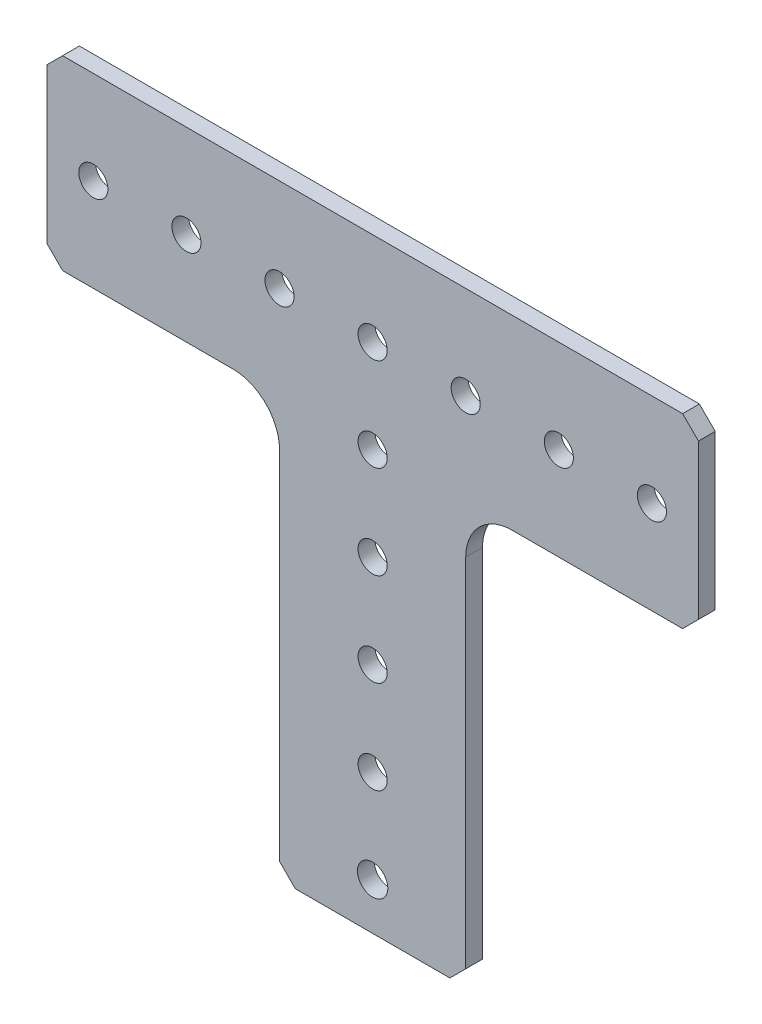
SolidWorks part; units mm, degrees
ref_plane "Front Plane" through (0, 0, 0) normal (0, 0, 1) x (1, 0, 0)
ref_plane "Top Plane" through (0, 0, 0) normal (0, 1, 0) x (1, 0, 0)
ref_plane "Right Plane" through (0, 0, 0) normal (1, 0, 0) x (0, 0, -1)
ref_plane "Plane1" through (0, 0, 2.286) normal (0, 0, 1) x (1, 0, 0)
sketch "Sketch1" plane through (0, 0, 2.286) normal (0, 0, 1) x (1, 0, 0)
  line L0 (12.7, -54.991) -> (12.7, -6.35)
  line L1 (19.05, 0) -> (42.291, 0)
  line L2 (42.291, 0) -> (44.45, 2.159)
  line L3 (44.45, 2.159) -> (44.45, 23.241)
  line L4 (44.45, 23.241) -> (42.291, 25.4)
  line L5 (42.291, 25.4) -> (-42.291, 25.4)
  line L6 (-42.291, 25.4) -> (-44.45, 23.241)
  line L7 (-44.45, 23.241) -> (-44.45, 2.159)
  line L8 (-44.45, 2.159) -> (-42.291, 0)
  line L9 (-42.291, 0) -> (-19.05, 0)
  line L10 (-12.7, -6.35) -> (-12.7, -54.991)
  line L11 (-12.7, -54.991) -> (-10.541, -57.15)
  line L12 (-10.541, -57.15) -> (10.541, -57.15)
  line L13 (10.541, -57.15) -> (12.7, -54.991)
  circle A11 centre (0, -50.8) radius 2.0701
  arc A12 (12.7, -6.35) -> (19.05, 0) centre (19.05, -6.35) cw
  arc A13 (-19.05, 0) -> (-12.7, -6.35) centre (-19.05, -6.35) cw
extrude "Boss-Extrude1" add sketch "Sketch1" against normal blind 2.286
hole_wizard "5/32 (0.15625) Diameter Hole1" positions "Sketch5" profile "Sketch4" hole size "5/32" standard "ANSI Inch" end condition through all
sketch "Sketch5" plane through (0, 0, 2.286) normal (0, 0, 1) x (1, 0, 0)
  point P0 (-38.1, 12.7)
  point P3 (-25.4, 12.7)
  point P6 (-12.7, 12.7)
  point P9 (0, 12.7)
  point P12 (12.7, 12.7)
  point P15 (25.4, 12.7)
  point P18 (38.1, 12.7)
  point P21 (0, 0)
  point P24 (0, -12.7)
  point P27 (0, -25.4)
  point P30 (0, -38.1)
  point P33 (0, -50.8)
sketch "Sketch4" plane through (-38.1, 12.7, 2.286) normal (1, 0, 0) x (0, -1, 0)
  line L0 (0, 0) -> (0, 2.286)
  line L1 (0, 2.286) -> (1.9844, 2.286)
  line L2 (1.9844, 2.286) -> (1.9844, 0)
  line L5 (1.9844, 0) -> (0, 0)
  line L11 (0, -6.35) -> (0, 107.95) construction
  dimension "Thru Hole Dia." = 3.9688
  dimension "Thru Hole Depth" = 2.286
